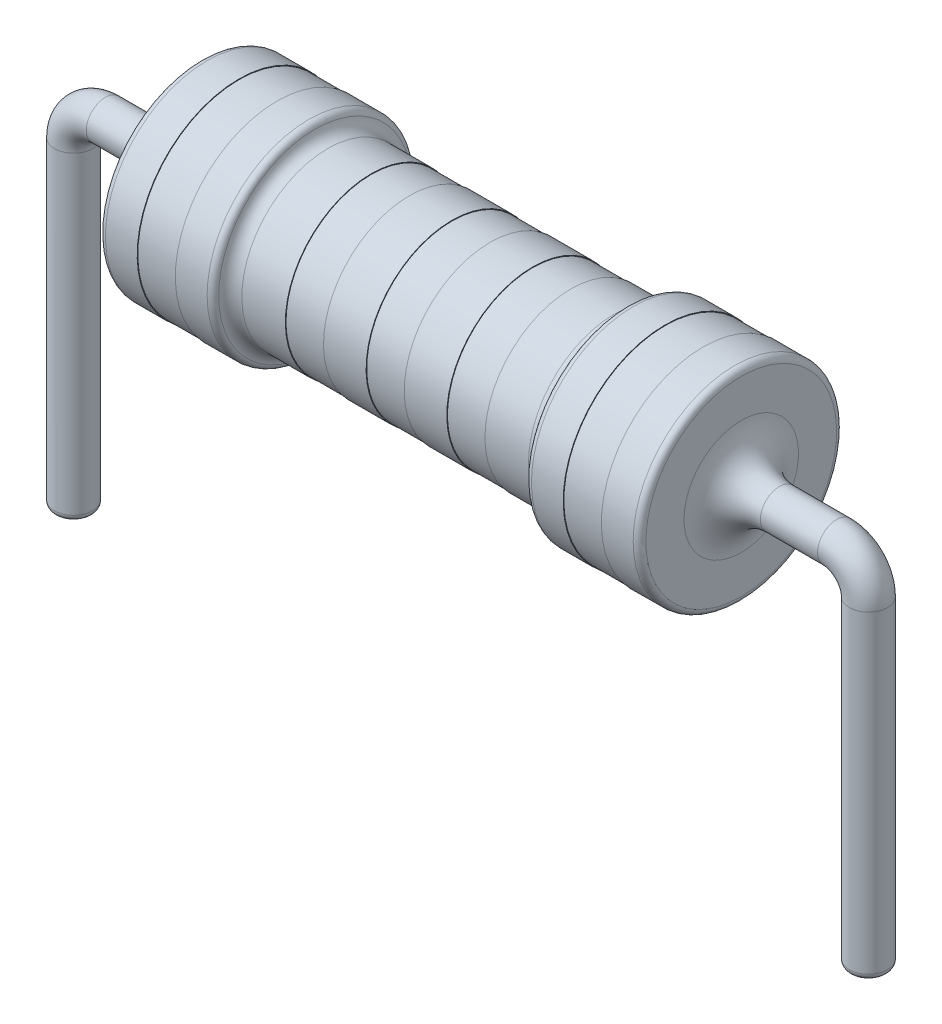
SolidWorks part; units mm, degrees
ref_plane "Front Plane" through (0, 0, 0) normal (0, 0, 1) x (1, 0, 0)
ref_plane "Top Plane" through (0, 0, 0) normal (0, 1, 0) x (1, 0, 0)
ref_plane "Right Plane" through (0, 0, 0) normal (1, 0, 0) x (0, 0, -1)
sketch "Sketch1" plane through (0, 0, 0) normal (0, 0, 1) x (1, 0, 0)
  line L0 (4.25, 0) -> (-4.25, 0)
  line L1 (4.25, 0) -> (4.25, -1.6)
  line L2 (4.25, -1.6) -> (3.65, -1.6)
  line L3 (3.65, -1.6) -> (3.65, -1.59)
  line L4 (3.65, -1.59) -> (3.05, -1.59)
  line L5 (3.05, -1.59) -> (3.05, -1.6)
  line L6 (3.05, -1.6) -> (2.45, -1.6)
  line L7 (2.45, -1.6) -> (2.45, -1.35)
  line L8 (2.45, -1.35) -> (1.5695, -1.35)
  line L9 (1.5695, -1.35) -> (1.5695, -1.34)
  line L10 (1.5695, -1.34) -> (0.9695, -1.34)
  line L11 (0.9695, -1.34) -> (0.9695, -1.35)
  line L12 (0.9695, -1.35) -> (0.3, -1.35)
  line L14 (-0.3, -1.34) -> (-0.3, -1.35)
  line L15 (-0.3, -1.34) -> (0.3, -1.34)
  line L16 (0.3, -1.34) -> (0.3, -1.35)
  line L17 (-0.9695, -1.35) -> (-0.3, -1.35)
  line L18 (-0.9695, -1.34) -> (-0.9695, -1.35)
  line L19 (-1.5695, -1.34) -> (-0.9695, -1.34)
  line L20 (-1.5695, -1.35) -> (-1.5695, -1.34)
  line L21 (-2.45, -1.35) -> (-1.5695, -1.35)
  line L22 (-2.45, -1.6) -> (-2.45, -1.35)
  line L23 (-3.05, -1.6) -> (-2.45, -1.6)
  line L24 (-3.05, -1.59) -> (-3.05, -1.6)
  line L25 (-3.65, -1.59) -> (-3.05, -1.59)
  line L26 (-3.65, -1.6) -> (-3.65, -1.59)
  line L27 (-4.25, -1.6) -> (-3.65, -1.6)
  line L28 (-4.25, 0) -> (-4.25, -1.6)
  dimension "D2" = 1.6
  dimension "D3" = 1.8
  dimension "D4" = 0.6
  dimension "D5" = 0.6
  dimension "D6" = 0.6
  dimension "D8" = 0.01
  dimension "D9" = 0.25
  dimension "D10" = 0.01
  dimension "D11" = 0.01
revolve "Revolve2" add sketch "Sketch1" angle 360 about L0
sketch "Sketch3" plane through (4.25, 0, 0) normal (1, 0, 0) x (0, 0, -1)
  circle A0 centre (0, 0) radius 0.3
sketch3d "3DSketch3"
  line L0 (4.25, 0, 0) -> (5.75, 0, 0)
  line L1 (6.25, -0.5, 0) -> (6.25, -5.5308, 0)
  arc A0 (6.25, -0.5, 0) -> (5.75, 0, 0) centre (5.75, -0.5, 0) ccw
  point P6 (6.25, 0, 0)
  point P7 (5.75, -0.5, 0.5)
  dimension "D2" = 0.5
  dimension "D1" = 2
sweep "Sweep2" add profiles "Sketch3" path "3DSketch3"
mirror "Mirror2" about plane through (0, 0, 0) normal (1, 0, 0) of "Sweep2"
fillet "Fillet10" radius 0.1 4 edges at (2.45, 1.6, 0) (-2.45, 1.6, 0) (4.25, 1.6, 0) (-4.25, 1.6, 0)
fillet "Fillet11" radius 0.2 2 edges at (2.45, 1.35, 0) (-2.45, 1.35, 0)
fillet "Fillet12" radius 0.6 2 edges at (-4.25, 0.3, 0) (4.25, 0.3, 0)
fillet "Fillet13" radius 0.1 2 edges at (6.55, -5.5308, 0) (-6.55, -5.5308, 0)
